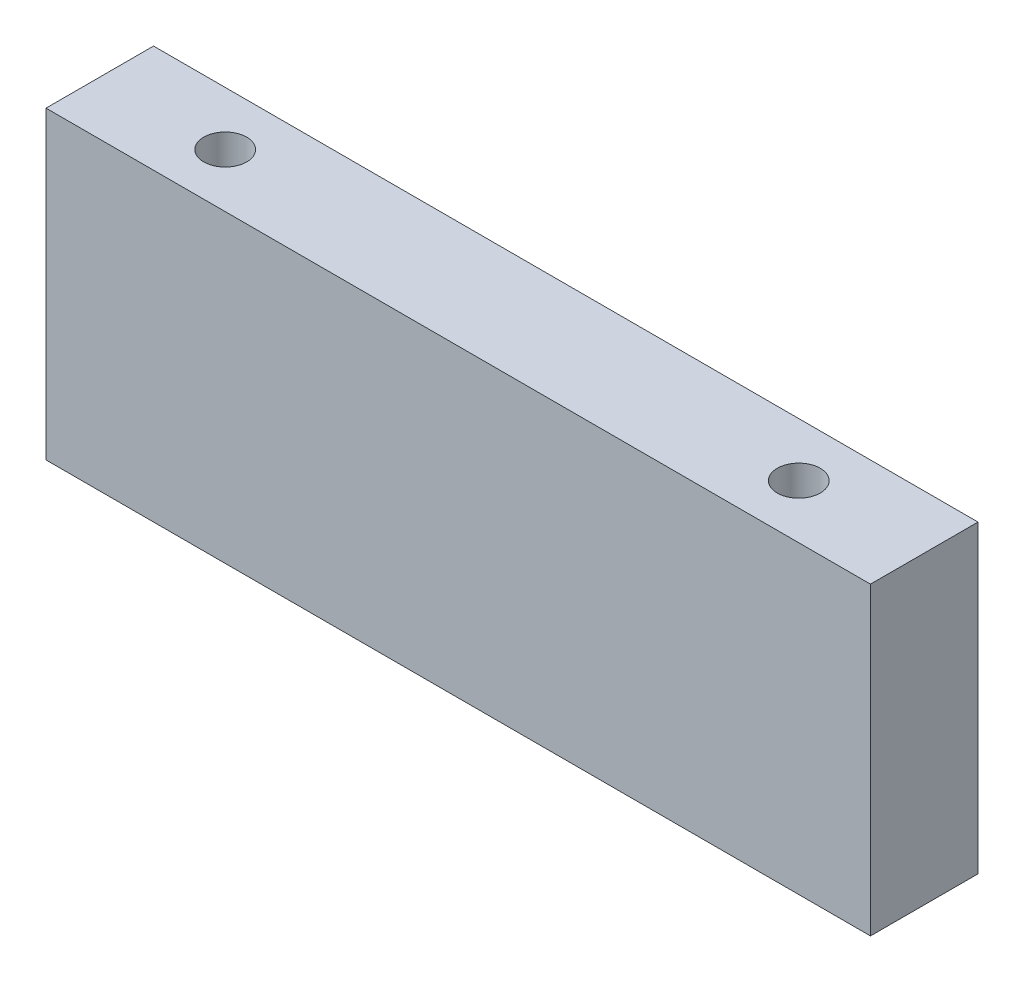
SolidWorks part; units mm, degrees
ref_plane "Front Plane" through (0, 0, 0) normal (0, 0, 1) x (1, 0, 0)
ref_plane "Top Plane" through (0, 0, 0) normal (0, 1, 0) x (1, 0, 0)
ref_plane "Right Plane" through (0, 0, 0) normal (1, 0, 0) x (0, 0, -1)
sketch "Sketch1" plane through (0, 0, 0) normal (0, 1, 0) x (1, 0, 0)
  line L1 (-57.5, -7.5) -> (57.5, -7.5)
  line L2 (-57.5, -7.5) -> (-57.5, 7.5)
  line L3 (-57.5, 7.5) -> (57.5, 7.5)
  line L4 (57.5, -7.5) -> (57.5, 7.5)
  line L5 (-57.5, -7.5) -> (57.5, 7.5) construction
  line L6 (-57.5, 7.5) -> (57.5, -7.5) construction
  point P0 (0, 0)
  dimension "D1" = 15
  dimension "D2" = 115
extrude "Boss-Extrude1" add sketch "Sketch1" along normal blind 42.5
sketch "Sketch2" plane through (0, 42.5, 0) normal (0, 1, 0) x (1, 0, 0)
  line L0 (-40, 0) -> (40, 0) construction
  circle A0 centre (-40, 0) radius 3
  circle A1 centre (40, 0) radius 3
  dimension "D2" = 6
  dimension "D1" = 80
extrude "Cut-Extrude1" cut sketch "Sketch2" against normal blind 42.5
